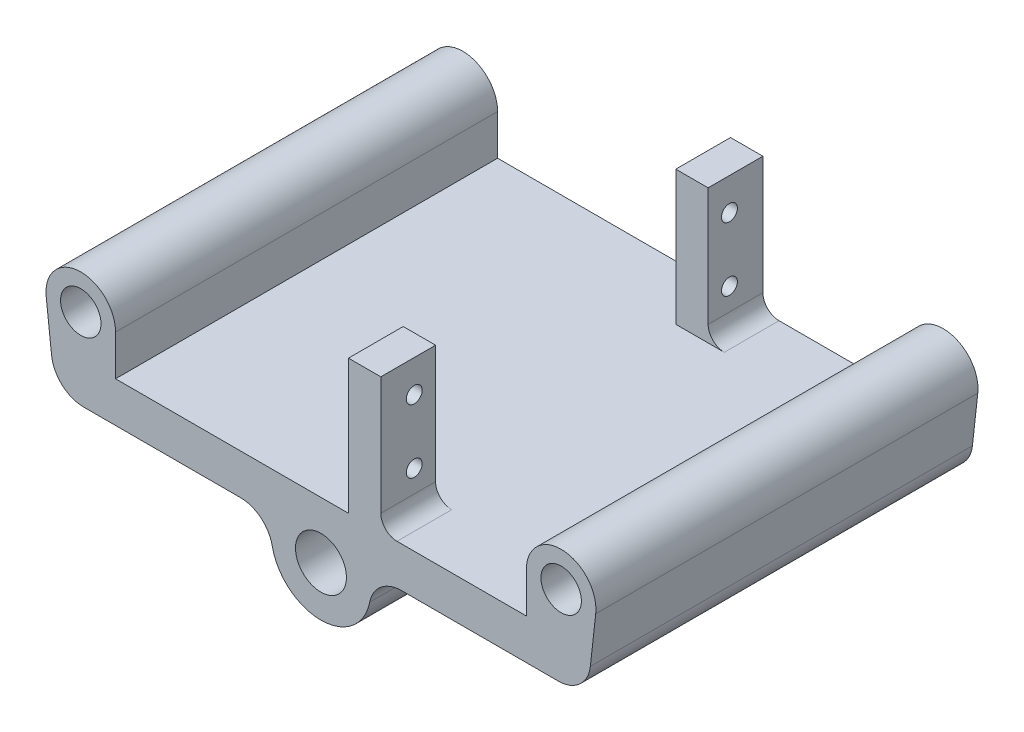
SolidWorks part; units mm, degrees
ref_plane "Front Plane" through (0, 0, 0) normal (0, 0, 1) x (1, 0, 0)
ref_plane "Top Plane" through (0, 0, 0) normal (0, 1, 0) x (1, 0, 0)
ref_plane "Right Plane" through (0, 0, 0) normal (1, 0, 0) x (0, 0, -1)
sketch "Sketch1" plane through (0, 0, 0) normal (0, 0, 1) x (1, 0, 0)
  line L0 (0, 0) -> (41.8013, 0)
  line L1 (41.8013, 0) -> (43.1465, 12.0964)
  line L2 (32.258, 12.7) -> (32.258, 6.35)
  line L3 (32.258, 6.35) -> (0, 6.35)
  line L4 (0, 6.35) -> (0, 0)
  line L5 (0, -430.8605) -> (0, 21112.1661) construction
  line L6 (37.719, 12.7) -> (0, 12.7) construction
  arc A0 (43.1465, 12.0964) -> (32.258, 12.7) centre (37.719, 12.7) ccw
  circle A1 centre (37.719, 12.7) radius 3.175
  circle A2 centre (0, 12.7) radius 46.228 construction
  dimension "D3" = 6.35
  dimension "D4" = 2.286
  dimension "D5" = 92.456
  dimension "D7" = 2.54
  dimension "D1" = 75.438
  dimension "D2" = 6.35
  dimension "D6" = 6.35
extrude "Boss-Extrude1" add sketch "Sketch1" along normal blind 60
sketch "Sketch2" plane through (0, 0, 0) normal (0, 0, -1) x (-1, 0, 0)
  line L0 (0, 0) -> (-41.8013, 0) construction
  line L1 (0, 0) -> (-41.8013, 0) construction
  circle A0 centre (-37.719, 12.7) radius 3.175 construction
  circle A1 centre (-37.719, 12.7) radius 3.175 construction
  circle A2 centre (0, -2.54) radius 4
  dimension "D2" = 8
  dimension "D1" = 15.24
extrude "Cut-Extrude1" cut sketch "Sketch2" against normal through all
sketch "Sketch3" plane through (0, 0, 0) normal (0, 0, -1) x (-1, 0, 0)
  line L0 (-3.09, 0) -> (-41.8013, 0) construction
  line L1 (-7.3854, 0) -> (-3.09, 0)
  line L2 (0, -10.35) -> (0, -6.54)
  arc A0 (-3.09, 0) -> (0, -6.54) centre (0, -2.54) ccw
  arc A1 (-7.3854, 0) -> (0, -10.35) centre (0, -2.54) ccw
  dimension "D1" = 3.81
extrude "Boss-Extrude2" add sketch "Sketch3" against normal up to surface (60 mm away) up to face at (21.8624, 6.4368, 60)
mirror "Mirror1" about plane through (0, 0, 0) normal (1, 0, 0) of "Boss-Extrude2", "Cut-Extrude1", "Boss-Extrude1"
sketch "Sketch5" plane through (0, 6.35, 0) normal (0, 1, 0) x (1, 0, 0)
  line L0 (6.858, -51.4) -> (6.858, -8.6) construction
  line L1 (4.318, 0) -> (9.398, 0)
  line L2 (4.318, 0) -> (4.318, -8.6)
  line L3 (4.318, -8.6) -> (9.398, -8.6)
  line L4 (9.398, 0) -> (9.398, -8.6)
  line L5 (4.318, -51.4) -> (9.398, -51.4)
  line L6 (4.318, -51.4) -> (4.318, -60)
  line L7 (4.318, -60) -> (9.398, -60)
  line L8 (9.398, -51.4) -> (9.398, -60)
  line L9 (6.858, -30) -> (32.258, -30) construction
  line L10 (32.258, -60) -> (32.258, 0) construction
  line L11 (32.258, 0) -> (-32.258, 0) construction
  dimension "D1" = 27.94
  dimension "D2" = 5.08
  dimension "D3" = 42.8
extrude "Boss-Extrude3" add sketch "Sketch5" along normal blind 21.1
sketch "Sketch6" plane through (9.398, 0, 0) normal (1, 0, 0) x (0, 0, -1)
  line L1 (0, 27.45) -> (0, 7.35) construction
  line L2 (-54.75, 22.4) -> (-5.25, 22.4) construction
  line L3 (-54.75, 22.4) -> (-54.75, 12.4) construction
  line L4 (-54.75, 12.4) -> (-5.25, 12.4) construction
  line L5 (-5.25, 22.4) -> (-5.25, 12.4) construction
  line L6 (0, 27.45) -> (0, 6.35) construction
  line L7 (-5.25, 17.4) -> (0, 17.4) construction
  line L8 (-30, 12.4) -> (-30, 6.35) construction
  line L9 (-60, 6.35) -> (0, 6.35) construction
  circle A4 centre (-54.75, 22.4) radius 1.25
  circle A5 centre (-5.25, 22.4) radius 1.25
  circle A6 centre (-5.25, 12.4) radius 1.25
  circle A7 centre (-54.75, 12.4) radius 1.25
  dimension "D3" = 2.5
  dimension "D1" = 10
  dimension "D2" = 20.1
  dimension "D4" = 49.5
extrude "Cut-Extrude2" cut sketch "Sketch6" against normal up to next
fillet "Fillet1" radius 2.54 2 edges at (9.398, 6.35, 4.3) (9.398, 6.35, 55.7)
fillet "Fillet3" radius 5.08 2 edges at (-7.3854, 0, 30) (7.3854, 0, 30)
fillet "Fillet4" radius 5.08 2 edges at (-41.8013, 0, 30) (41.8013, 0, 30)
